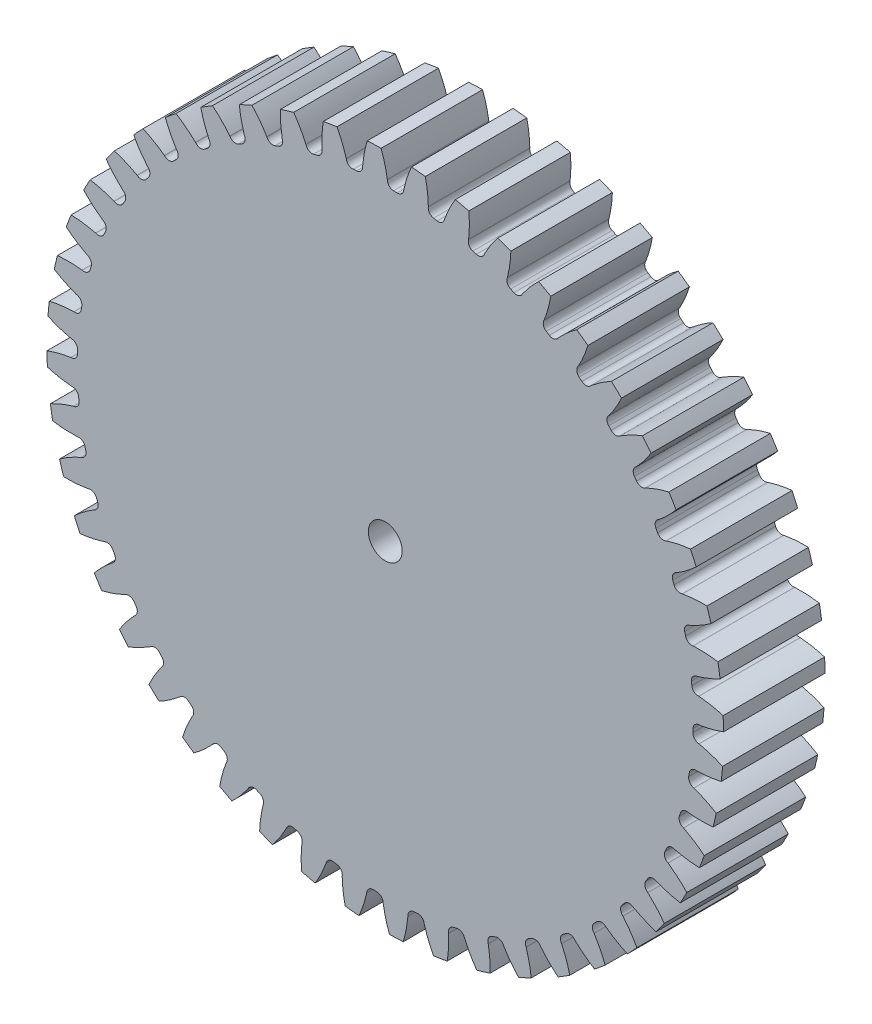
SolidWorks part; units mm, degrees
ref_plane "Front" through (0, 0, 0) normal (0, 0, 1) x (1, 0, 0)
ref_plane "Top" through (0, 0, 0) normal (0, 1, 0) x (1, 0, 0)
ref_plane "Right" through (0, 0, 0) normal (1, 0, 0) x (0, 0, -1)
sketch "Sketch1" plane through (0, 0, 0) normal (0, 0, 1) x (1, 0, 0)
  line L0 (-609.6, 0) -> (609.6, 0) construction
  circle A0 centre (0, 0) radius 31.75
  circle A1 centre (0, 0) radius 30.48 construction
  circle A3 centre (0, 0) radius 28.8925 construction
  dimension "D3" = 1.27
  dimension "D1" = 2.8575
extrude "Boss-Extrude1" add sketch "Sketch1" against normal blind 9.525
sketch "Sketch3" plane through (0, 0, 0) normal (0, 0, 1) x (1, 0, 0)
  line L0 (0, 0) -> (0, 31.75) construction
  line L1 (-7.3885, 28.5692) -> (0, 30.48)
  line L2 (-9.5921, 30.48) -> (9.5921, 30.48) construction
  line L3 (-9.2865, 28.0783) -> (9.2865, 32.8817) construction
  line L4 (-7.3885, 28.5692) -> (0, 0) construction
  line L5 (-18.8456, 22.7076) -> (0, 0) construction
  line L6 (-18.8456, 22.7076) -> (-3.0091, 35.8506) construction
  line L7 (-5.1519, 29.0559) -> (0, 0) construction
  line L8 (-5.1519, 29.0559) -> (0.1081, 29.9886) construction
  arc A0 (-7.3885, 28.5692) -> (-18.8456, 22.7076) centre (0, 0) ccw
  circle A1 centre (0, 0) radius 30.48 construction
  circle A2 centre (0, 0) radius 29.5091 construction
  arc A3 (-7.3885, 28.5692) -> (-5.1519, 29.0559) centre (0, 0) cw
  circle A4 centre (0, 0) radius 31.75 construction
  point P6 (0, 30.48)
  dimension "D1" = 7.6316
  dimension "Pressure Angle" = 14.5
  dimension "D2" = 12.9737
  dimension "D3" = 20.5799
  dimension "D4" = 2.2895
  dimension "D5" = 5.3421
sketch "Sketch4" plane through (0, 0, 0) normal (0, 0, 1) x (1, 0, 0)
  line L0 (0, 0) -> (0.9967, 30.4474) construction
  line L1 (0.192, 29.5085) -> (0.192, 28.8919)
  line L2 (0, 30.48) -> (1.9935, 30.4147) construction
  line L3 (1.7384, 29.4579) -> (1.698, 28.8426)
  line L4 (0.192, 28.8919) -> (0, 0) construction
  line L5 (0, 0) -> (0, 31.75) construction
  line L6 (-18.8456, 22.7076) -> (-3.0091, 35.8506) construction
  line L7 (-18.8456, 22.7076) -> (-3.0091, 35.8506) construction
  arc A0 (1.698, 28.8426) -> (0.192, 28.8919) centre (0, 0) ccw
  arc A1 (0, 30.48) -> (1.9935, 30.4147) centre (0, 0) cw construction
  circle A2 centre (0, 0) radius 30.48 construction
  circle A3 centre (0, 0) radius 29.5091 construction
  circle A4 centre (0, 0) radius 28.8925 construction
  arc A5 (5.3474, 35.577) -> (-3.0091, 35.8506) centre (0, 0) ccw
  spline S0 degree 2 poles (-3.0091, 35.8506) (-0.3489, 33.0435) (0.192, 29.5085) knots 0 0 0 1 1 1
  spline S1 degree 2 poles (5.3474, 35.577) (2.5093, 32.95) (1.7384, 29.4579) knots 0 0 0 1 1 1
  dimension "D1" = 1.9949
extrude "Cut-Extrude1" cut sketch "Sketch4" against normal through all
fillet "Fillet1" radius 0.5985 2 edges at (1.698, 28.8426, -4.7625) (0.192, 28.8919, -4.7625)
pattern_circular "CirPattern1" count 48 over 360 about axis through (0, 0, -9.525) along (0, 0, 1) of "Cut-Extrude1", "Fillet1"
sketch "Sketch5" plane through (0, 0, 0) normal (0, 0, 1) x (1, 0, 0)
  line L0 (0, 2.7788) -> (0, 0) construction
  line L1 (-1.1906, 1.05) -> (1.1906, 1.05) construction
  line L2 (-1.1906, 1.05) -> (-1.1906, 2.7788) construction
  line L3 (-1.1906, 2.7788) -> (1.1906, 2.7788) construction
  line L4 (1.1906, 1.05) -> (1.1906, 2.7788) construction
  line L5 (-1.1906, 1.05) -> (1.1906, 2.7788) construction
  line L6 (-1.1906, 2.7788) -> (1.1906, 1.05) construction
  circle A0 centre (0, 0) radius 1.5875
  point P3 (0, 1.9144)
  point P8 (0, 1.5875)
  point P9 (0, -1.5875)
  dimension "Bore Min" = 3.175
  dimension "Keyway Wd" = 2.3813
  dimension "Keyway Dpt." = 1.1913
extrude "Cut-Extrude2" cut sketch "Sketch5" against normal through all
sketch "Pitch Dia" plane through (0, 0, 0) normal (0, 0, 1) x (1, 0, 0)
  circle A0 centre (0, 0) radius 30.48 construction
  circle A1 centre (0, 0) radius 30.48 construction
equation "\"D1@Sketch4\" = 1.5708/(\"Number of Teeth@Sketch1\"/\"Ptich Dia@Sketch1\")"
equation "\"D1@CirPattern1\" = \"Number of Teeth@Sketch1\""
equation "\"D1@Fillet1\" = \"D1@Sketch4\"*.3"
equation "\"D1@Sketch1\" = 2.250/(\"Number of Teeth@Sketch1\"/\"Ptich Dia@Sketch1\")"
